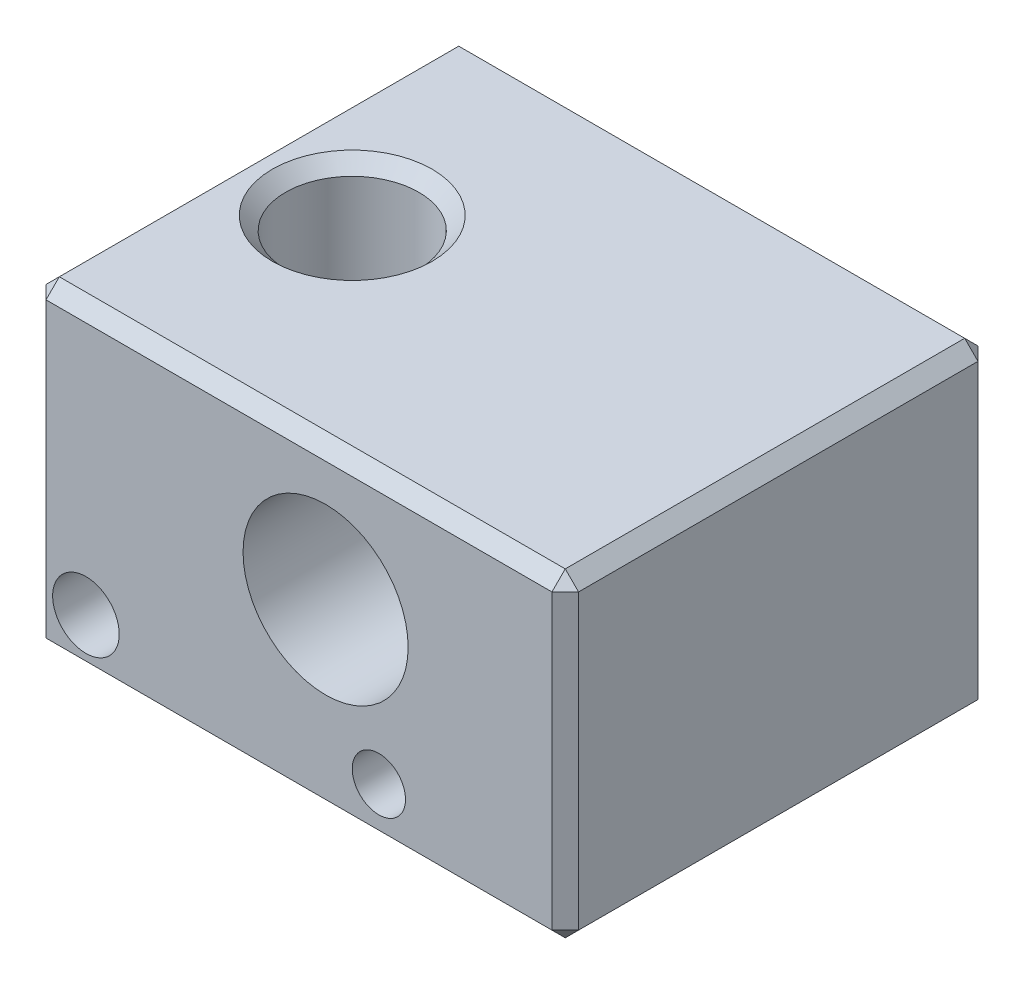
SolidWorks part; units mm, degrees
material "AISI 316 Annealed Stainless Steel Bar (SS)"
ref_plane "Front Plane" through (0, 0, 0) normal (0, 0, 1) x (1, 0, 0)
ref_plane "Top Plane" through (0, 0, 0) normal (0, 1, 0) x (1, 0, 0)
ref_plane "Right Plane" through (0, 0, 0) normal (1, 0, 0) x (0, 0, -1)
sketch "Sketch1" plane through (0, 0, 0) normal (0, 1, 0) x (1, 0, 0)
  line L1 (-10, -8) -> (10, -8)
  line L2 (-10, -8) -> (-10, 8)
  line L3 (-10, 8) -> (10, 8)
  line L4 (10, -8) -> (10, 8)
  line L5 (-10, -8) -> (10, 8) construction
  line L6 (-10, 8) -> (10, -8) construction
  point P0 (0, 0)
  dimension "D1" = 20
  dimension "D2" = 16
extrude "Boss-Extrude1" add sketch "Sketch1" along normal blind 12 contours L2 L3 L4 L1
sketch "Sketch2" plane through (0, 0, 8) normal (0, 0, 1) x (1, 0, 0)
  line L0 (-10, 12) -> (-10, 0) construction
  line L1 (-10, 0) -> (10, 0) construction
  circle A0 centre (1, 7) radius 3.1
  circle A1 centre (3, 2) radius 1
  dimension "D2" = 6.2
  dimension "D4" = 13
  dimension "D6" = 2
  dimension "D1" = 11
  dimension "D3" = 7
  dimension "D5" = 2
extrude "Cut-Extrude1" cut sketch "Sketch2" against normal through all
hole_wizard "Ø2.5 (2.5) Diameter Hole1" positions "Sketch4" profile "Sketch3" hole size "Ø2.5" standard "ANSI Metric"
sketch "Sketch4" plane through (0, 0, 8) normal (0, 0, 1) x (1, 0, 0)
  line L0 (-10, 12) -> (-10, 0) construction
  line L1 (-10, 0) -> (10, 0) construction
  point P0 (-8, 2)
  dimension "D1" = 2
  dimension "D2" = 2
sketch "Sketch3" plane through (-8, 2, 8) normal (1, 0, 0) x (0, -1, 0)
  line L0 (0, 0) -> (0, 4.5)
  line L1 (0, 4.5) -> (1.25, 4.5)
  line L2 (1.25, 4.5) -> (1.25, 0)
  line L5 (1.25, 0) -> (0, 0)
  line L10 (0, 4.5) -> (-1.25, 4.5) construction
  line L11 (0, -6.35) -> (0, 107.95) construction
  dimension "Hole Dia." = 2.5
  dimension "Hole Depth" = 4.5
  dimension "Drill Angle" = 180
hole_wizard "Tap Drill for M6x1.0 Tap1" positions "Sketch7" profile "Sketch6" hole size "M6x1.0" standard "ANSI Metric" end condition through all
sketch "Sketch7" plane through (0, 12, 0) normal (0, 1, 0) x (1, 0, 0)
  line L0 (-10, -8) -> (-10, 8) construction
  point P0 (-6, 0)
  dimension "D1" = 4
sketch "Sketch6" plane through (-6, 12, 0) normal (1, 0, 0) x (0, 0, 1)
  line L0 (0, 0) -> (0, 12)
  line L1 (0, 12) -> (2.5, 12)
  line L2 (2.5, 12) -> (2.5, 0)
  line L5 (2.5, 0) -> (0, 0)
  line L11 (0, -6.35) -> (0, 107.95) construction
  dimension "Thru Hole Dia." = 5
  dimension "Thru Hole Depth" = 12
hole_wizard "Tap Drill for M3x0.5 Tap1" positions "Sketch9" profile "Sketch8" hole size "M3x0.5" standard "ANSI Metric"
sketch "Sketch9" plane through (0, 0, 0) normal (0, -1, 0) x (-1, 0, 0)
  line L0 (10, -8) -> (10, 8) construction
  point P0 (0, 0)
  dimension "D1" = 10
sketch "Sketch8" plane through (0, 0, 0) normal (1, 0, 0) x (0, 0, -1)
  line L0 (0, 0) -> (0, 7.7501)
  line L1 (0, 7.7501) -> (1.25, 6.999)
  line L2 (1.25, 6.999) -> (1.25, 0)
  line L5 (1.25, 0) -> (0, 0)
  line L10 (0, 7.7501) -> (-1.25, 6.999) construction
  line L11 (0, -6.35) -> (0, 107.95) construction
  dimension "Hole Dia." = 2.5
  dimension "Hole Depth" = 6.999
  dimension "Drill Angle" = 118
chamfer "Chamfer1" distance 0.5 angle 45 15 edges at (-6, 0, 2.5) (0, 0, -1.25) (-10, 6, -8) (-10, 6, 8) (10, 6, 8) (10, 0, 0) (0, 0, 8) (-10, 0, 0) (0, 0, -8) (10, 6, -8) (-10, 12, 0) (0, 12, -8) (10, 12, 0) (0, 12, 8) (-6, 12, 2.5)
